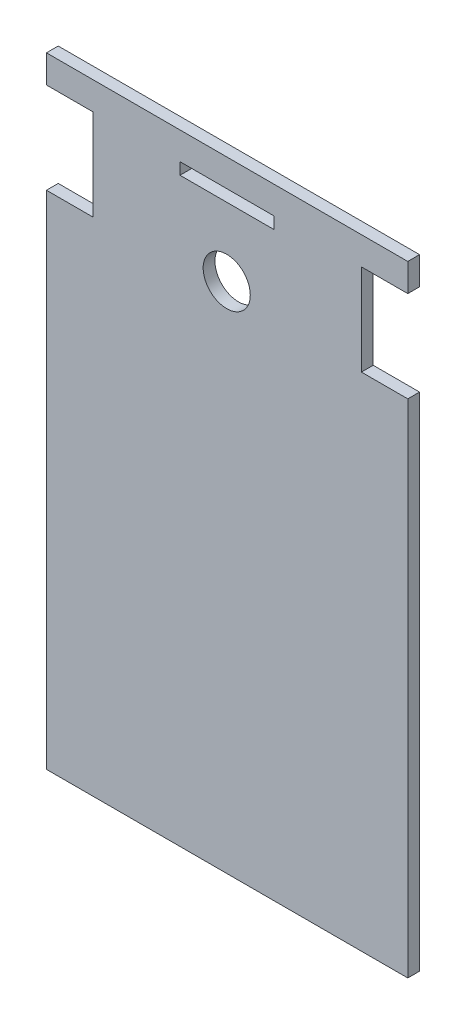
SolidWorks part; units mm, degrees
ref_plane "Alzado" through (0, 0, 0) normal (0, 0, 1) x (1, 0, 0)
ref_plane "Planta" through (0, 0, 0) normal (0, 1, 0) x (1, 0, 0)
ref_plane "Vista lateral" through (0, 0, 0) normal (1, 0, 0) x (0, 0, -1)
sketch "Model" plane through (0, 0, 0) normal (0, 0, 1) x (1, 0, 0)
  line L0 (54, 89) -> (54, 81.9)
  line L1 (146, 81.9) -> (146, 89)
  line L2 (134.2, 81.9) -> (146, 81.9)
  line L3 (134.2, 58.7) -> (134.2, 81.9)
  line L4 (146, 58.7) -> (134.2, 58.7)
  line L5 (146, -69) -> (146, 58.7)
  line L6 (54, -69) -> (146, -69)
  line L7 (54, 58.7) -> (54, -69)
  line L8 (146, 89) -> (54, 89)
  line L9 (65.8, 58.7) -> (54, 58.7)
  line L10 (65.8, 81.9) -> (65.8, 58.7)
  line L11 (54, 81.9) -> (65.8, 81.9)
  line L12 (88, 79) -> (112, 79)
  line L13 (88, 82) -> (88, 79)
  line L14 (112, 82) -> (88, 82)
  line L15 (112, 79) -> (112, 82)
  circle A0 centre (99.8993, 61.5296) radius 6
extrude "Saliente-Extruir1" add sketch "Model" along normal blind 3
